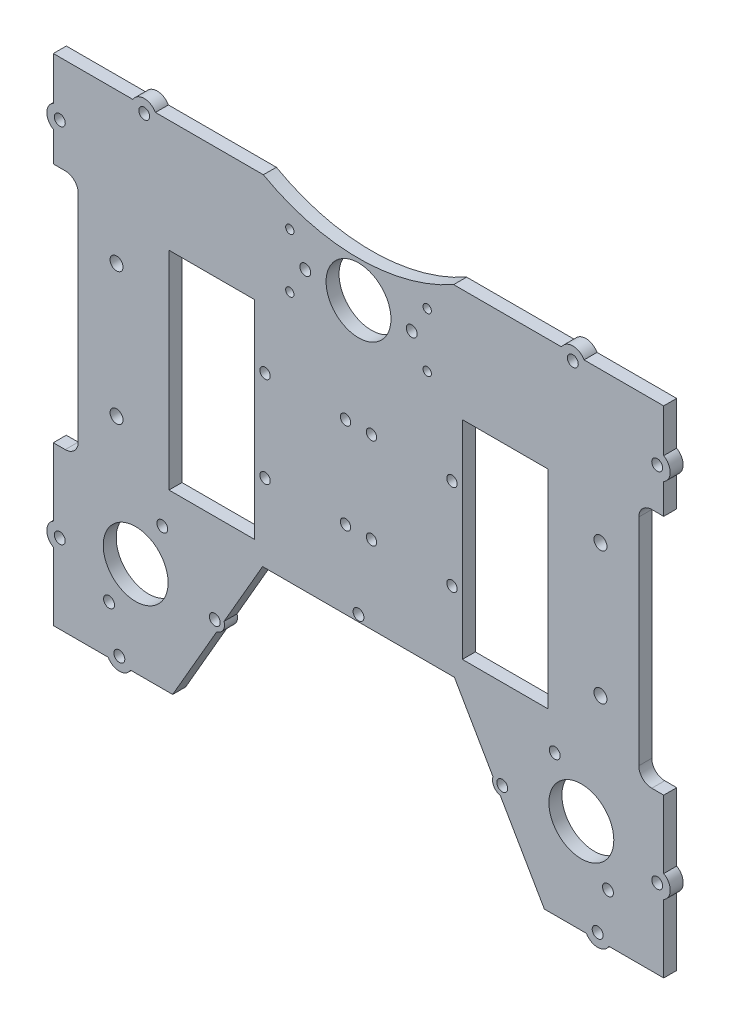
SolidWorks part; units mm, degrees
ref_plane "Front Plane" through (0, 0, 0) normal (0, 0, 1) x (1, 0, 0)
ref_plane "Top Plane" through (0, 0, 0) normal (0, 1, 0) x (1, 0, 0)
ref_plane "Right Plane" through (0, 0, 0) normal (1, 0, 0) x (0, 0, -1)
sketch "Sketch2" plane through (0, 0, 0) normal (0, 0, 1) x (1, 0, 0)
  line L0 (118.8549, -90.2648) -> (131.3549, -68.6142)
  line L1 (131.3549, -68.6142) -> (131.3549, -34.0686)
  line L2 (131.3549, -23.1598) -> (131.3549, 57.175)
  line L3 (131.3549, 68.0837) -> (131.3549, 77.6294)
  line L4 (118.8549, 99.28) -> (102.5756, 108.6789)
  line L5 (93.1284, 114.1332) -> (71.1618, 126.8156)
  line L6 (-68.452, 126.8156) -> (-90.4186, 114.1332)
  line L7 (-99.8658, 108.6789) -> (-116.1451, 99.28)
  line L8 (-128.6451, 77.6294) -> (-128.6451, 68.0837)
  line L9 (-128.6451, 57.175) -> (-128.6451, -23.1598)
  line L10 (-128.6451, -34.0686) -> (-128.6451, -68.6142)
  line L11 (-128.6451, -68.6142) -> (-116.1451, -90.2648)
  line L12 (-116.1451, -90.2648) -> (-48.6451, -129.236)
  line L13 (-48.6451, -129.236) -> (51.3549, -129.236)
  line L14 (51.3549, -129.236) -> (118.8549, -90.2648)
  line L15 (-90.4186, 114.1332) -> (-99.8658, 108.6789)
  line L16 (-128.6451, 68.0837) -> (-128.6451, 57.175)
  line L17 (-128.6451, -23.1598) -> (-128.6451, -34.0686)
  line L18 (131.3549, 68.0837) -> (131.3549, 57.175)
  line L19 (93.1284, 114.1332) -> (102.5756, 108.6789)
  line L20 (131.3549, -23.1598) -> (131.3549, -34.0686)
  arc A2 (131.3549, 77.6294) -> (118.8549, 99.28) centre (106.3549, 77.6294) ccw
  arc A4 (71.1618, 126.8156) -> (69.8628, 127.3391) centre (68.6618, 122.4855) ccw
  arc A5 (-67.153, 127.3391) -> (69.8628, 127.3391) centre (1.3549, 141.7152) ccw
  arc A6 (-67.153, 127.3391) -> (-68.452, 126.8156) centre (-65.952, 122.4855) ccw
  arc A8 (-116.1451, 99.28) -> (-128.6451, 77.6294) centre (-103.6451, 77.6294) ccw
extrude "Boss-Extrude1" add sketch "Sketch2" along normal blind 5
sketch "Sketch4" plane through (0, 0, 5) normal (0, 0, 1) x (1, 0, 0)
  line L0 (1.3549, 141.7152) -> (1.3549, 46.7152) construction
  line L11 (51.3549, -129.236) -> (118.8549, -90.2648)
  line L12 (118.8549, -90.2648) -> (131.3549, -68.6142)
  line L13 (131.3549, -68.6142) -> (131.3549, 77.6294)
  line L14 (118.8549, 99.28) -> (71.1618, 126.8156)
  line L15 (-68.452, 126.8156) -> (-116.1451, 99.28)
  line L16 (-128.6451, 77.6294) -> (-128.6451, -68.6142)
  line L17 (-128.6451, -68.6142) -> (-116.1451, -90.2648)
  line L18 (-116.1451, -90.2648) -> (-48.6451, -129.236)
  line L19 (-48.6451, -129.236) -> (51.3549, -129.236)
  line L23 (76.3249, 123.8347) -> (71.1618, 126.8156)
  line L24 (-68.452, 126.8156) -> (-73.6152, 123.8347)
  arc A1 (-73.6152, 123.8347) -> (76.3249, 123.8347) centre (1.3549, 121.7152) ccw
  arc A7 (131.3549, 77.6294) -> (118.8549, 99.28) centre (106.3549, 77.6294) ccw
  arc A8 (71.1618, 126.8156) -> (69.8628, 127.3391) centre (68.6618, 122.4855) ccw
  arc A9 (-67.153, 127.3391) -> (69.8628, 127.3391) centre (1.3549, 141.7152) ccw
  arc A10 (-67.153, 127.3391) -> (-68.452, 126.8156) centre (-65.952, 122.4855) ccw
  arc A11 (-116.1451, 99.28) -> (-128.6451, 77.6294) centre (-103.6451, 77.6294) ccw
  arc A13 (71.1618, 126.8156) -> (69.8628, 127.3391) centre (68.6618, 122.4855) ccw
  arc A15 (-67.153, 127.3391) -> (-68.452, 126.8156) centre (-65.952, 122.4855) ccw
  arc A17 (-67.153, 127.3391) -> (69.8628, 127.3391) centre (1.3549, 141.7152) ccw
  dimension "D1" = 150
  dimension "D2" = 20
  dimension "D3" = 0
extrude "Cut-Extrude1" cut sketch "Sketch4" against normal blind 5
fillet "Fillet1" radius 10 2 edges at (76.3249, 123.8347, 2.5) (-73.6152, 123.8347, 2.5)
sketch "Sketch6" plane through (0, 0, 5) normal (0, 0, 1) x (1, 0, 0)
  line L0 (-128.6451, -68.6142) -> (-128.6451, -169.9521)
  line L1 (-128.6451, -169.9521) -> (131.3549, -169.9521)
  line L2 (131.3549, -68.6142) -> (131.3549, -169.9521)
  line L12 (118.8549, 99.28) -> (90.1091, 115.8764)
  line L13 (-87.3994, 115.8764) -> (-116.1451, 99.28)
  line L14 (-128.6451, 77.6294) -> (-128.6451, -68.6142)
  line L15 (-128.6451, -68.6142) -> (-116.1451, -90.2648)
  line L16 (-116.1451, -90.2648) -> (-48.6451, -129.236)
  line L17 (-48.6451, -129.236) -> (51.3549, -129.236)
  line L18 (51.3549, -129.236) -> (118.8549, -90.2648)
  line L19 (118.8549, -90.2648) -> (131.3549, -68.6142)
  line L20 (131.3549, -68.6142) -> (131.3549, 77.6294)
  line L24 (-128.6451, -68.6142) -> (-116.1451, -90.2648)
  line L25 (-116.1451, -90.2648) -> (-48.6451, -129.236)
  line L26 (-48.6451, -129.236) -> (51.3549, -129.236)
  line L27 (51.3549, -129.236) -> (118.8549, -90.2648)
  line L28 (118.8549, -90.2648) -> (131.3549, -68.6142)
  arc A5 (90.1091, 115.8764) -> (75.2557, 108.9219) centre (85.1091, 107.2161) ccw
  arc A6 (-72.5459, 108.9219) -> (75.2557, 108.9219) centre (1.3549, 121.7152) ccw
  arc A7 (-72.5459, 108.9219) -> (-87.3994, 115.8764) centre (-82.3994, 107.2161) ccw
  arc A8 (-116.1451, 99.28) -> (-128.6451, 77.6294) centre (-103.6451, 77.6294) ccw
  arc A9 (131.3549, 77.6294) -> (118.8549, 99.28) centre (106.3549, 77.6294) ccw
  dimension "D1" = 0
extrude "Boss-Extrude2" add sketch "Sketch6" against normal blind 5
sketch "Sketch7" plane through (0, 0, 5) normal (0, 0, 1) x (1, 0, 0)
  line L0 (-116.2134, 18.7152) -> (-116.2151, -61.2848)
  line L3 (118.9232, 18.7152) -> (118.9249, -61.2848)
  line L18 (-71.6451, -21.2848) -> (-128.6451, -21.2848) construction
  line L20 (-128.6451, 77.6294) -> (-128.6451, -169.9521) construction
  line L21 (-116.2134, 18.7152) -> (-116.1451, 99.28)
  line L22 (-116.2151, -61.2848) -> (-116.2151, -169.9521)
  line L23 (-128.6451, -169.9521) -> (131.3549, -169.9521) construction
  line L27 (1.3549, -169.9521) -> (1.3549, -118.8458) construction
  line L28 (74.3549, -21.2848) -> (131.3549, -21.2848) construction
  line L32 (118.9249, -61.2848) -> (118.9249, -169.9521)
  line L33 (118.9232, 18.7152) -> (118.8549, 99.28)
  line L52 (118.9249, -169.9521) -> (131.3549, -169.9521)
  line L57 (118.8549, 99.28) -> (90.1091, 115.8764)
  line L58 (-87.3994, 115.8764) -> (-116.1451, 99.28)
  line L59 (-128.6451, 77.6294) -> (-128.6451, -169.9521)
  line L60 (-128.6451, -169.9521) -> (131.3549, -169.9521)
  line L61 (131.3549, -169.9521) -> (131.3549, 77.6294)
  line L64 (-128.6451, 77.6294) -> (-128.6451, -169.9521)
  line L66 (131.3549, -169.9521) -> (131.3549, 77.6294)
  line L68 (-128.6451, -169.9521) -> (131.3549, -169.9521)
  arc A69 (90.1091, 115.8764) -> (75.2557, 108.9219) centre (85.1091, 107.2161) ccw
  arc A70 (-72.5459, 108.9219) -> (75.2557, 108.9219) centre (1.3549, 121.7152) ccw
  arc A71 (-72.5459, 108.9219) -> (-87.3994, 115.8764) centre (-82.3994, 107.2161) ccw
  arc A72 (-116.1451, 99.28) -> (-128.6451, 77.6294) centre (-103.6451, 77.6294) ccw
  arc A73 (131.3549, 77.6294) -> (118.8549, 99.28) centre (106.3549, 77.6294) ccw
  arc A77 (-116.1451, 99.28) -> (-128.6451, 77.6294) centre (-103.6451, 77.6294) ccw
  arc A78 (131.3549, 77.6294) -> (118.8549, 99.28) centre (106.3549, 77.6294) ccw
  dimension "D11" = 0
extrude "Cut-Extrude3" cut sketch "Sketch7" against normal blind 10
sketch "Sketch8" plane through (0, 0, 5) normal (0, 0, 1) x (1, 0, 0)
  line L0 (1.3549, 46.7152) -> (1.3549, -169.9521) construction
  line L1 (-116.2151, -169.9521) -> (118.9249, -169.9521) construction
  line L3 (-19.1451, -101.2848) -> (21.8549, -101.2848) construction
  arc A0 (-72.5459, 108.9219) -> (75.2557, 108.9219) centre (1.3549, 121.7152) ccw construction
  circle A1 centre (1.3549, -101.2848) radius 12.5
  circle A2 centre (21.8549, -101.2848) radius 2.1
  circle A3 centre (-19.1451, -101.2848) radius 2.1
  dimension "D1" = 25
  dimension "D2" = 4.2
  dimension "D3" = 4.2
  dimension "D4" = 20.5
  dimension "D5" = 20.5
extrude "Cut-Extrude4" cut sketch "Sketch8" against normal blind 10
sketch "Sketch9" plane through (0, 0, 5) normal (0, 0, 1) x (1, 0, 0)
  line L0 (-101.2143, -21.2848) -> (103.924, -21.2848) construction
  line L1 (1.3549, -122.073) -> (1.3549, -169.9521) construction
  line L2 (-116.2151, -169.9521) -> (118.9249, -169.9521) construction
  line L6 (94.0402, -122.073) -> (118.9249, -109.2181)
  line L11 (-116.2151, -102.073) -> (-85.0382, -122.073)
  line L12 (-85.0382, -122.073) -> (94.0402, -122.073)
  line L15 (1.3549, 101.5642) -> (-58.9528, 70.4107) [skipped]
  line L16 (118.9249, 33.6852) -> (61.7912, 70.3364) [skipped]
  line L17 (118.9249, -102.073) -> (122.099, -34.2682) [skipped]
  line L18 (-116.2151, 33.6852) -> (-122.5633, -101.9245) [skipped]
  line L25 (-116.2134, 18.7152) -> (-116.2151, -61.2848)
  line L26 (-116.2134, 18.7152) -> (-116.2151, -61.2848)
  line L27 (118.9249, -61.2848) -> (118.9232, 18.7152)
  line L28 (118.9249, -61.2848) -> (118.9232, 18.7152)
  line L29 (-116.2151, -169.9521) -> (118.9249, -169.9521)
  line L30 (-116.2151, -169.9521) -> (118.9249, -169.9521)
  line L32 (-116.2151, -61.2848) -> (-116.2151, -169.9521)
  line L34 (118.9249, -169.9521) -> (118.9249, -61.2848)
  line L38 (118.9232, 18.7152) -> (118.8549, 99.28)
  line L39 (118.8549, 99.28) -> (90.1091, 115.8764)
  line L40 (-87.3994, 115.8764) -> (-116.1451, 99.28)
  line L41 (-116.1451, 99.28) -> (-116.2134, 18.7152)
  line L45 (-116.2151, -102.073) -> (-116.2151, -169.9521)
  line L47 (118.9249, -169.9521) -> (118.9249, -109.2181)
  arc A0 (1.3549, -154.8094) -> (83.9707, -122.073) centre (1.3549, -34.1939) ccw construction
  arc A4 (90.1091, 115.8764) -> (75.2557, 108.9219) centre (85.1091, 107.2161) ccw
  arc A5 (-72.5459, 108.9219) -> (75.2557, 108.9219) centre (1.3549, 121.7152) ccw
  arc A6 (-72.5459, 108.9219) -> (-87.3994, 115.8764) centre (-82.3994, 107.2161) ccw
  line M59 (-116.2151, -61.2848) -> (-116.2151, -169.9521)
  line M60 (-116.2151, -169.9521) -> (118.9249, -169.9521)
  line M61 (118.9249, -169.9521) -> (118.9249, -61.2848)
  dimension "D1" = 20
  dimension "D2" = 0
extrude "Cut-Extrude5" cut sketch "Sketch9" against normal blind 10 contours L12 L11 L6 M59 M60 M61
fillet "Fillet4" radius 10 2 edges at (118.8549, 99.28, 2.5) (-116.1451, 99.28, 2.5)
sketch "Sketch11" plane through (0, 0, 5) normal (0, 0, 1) x (1, 0, 0)
  line L0 (115.3826, -104.3454) -> (87.748, -122.073)
  line L1 (94.0402, -122.073) -> (-85.0382, -122.073) construction
  line L2 (115.3826, -104.3454) -> (118.9249, -102.073)
  line L3 (118.9249, -61.2848) -> (118.9249, -109.2181) construction
  line L4 (118.9249, -102.073) -> (118.9249, -109.2181)
  line L5 (118.9249, -109.2181) -> (94.0402, -122.073)
  line L6 (94.0402, -122.073) -> (87.748, -122.073)
extrude "Cut-Extrude6" cut sketch "Sketch11" against normal blind 55
sketch "Sketch12" plane through (0, 0, 5) normal (0, 0, 1) x (1, 0, 0)
  line L4 (-87.3994, 115.8764) -> (-87.3994, 35.8764) construction
  line L5 (1.3549, 46.7152) -> (1.3549, 28.9079) construction
  line L6 (90.1091, 115.8764) -> (90.1091, 35.8764) construction
  circle A4 centre (-87.3994, 75.8764) radius 12.5
  circle A5 centre (-87.3994, 96.3764) radius 2.1
  circle A6 centre (-87.3994, 55.3764) radius 2.1
  arc A7 (-72.5459, 108.9219) -> (75.2557, 108.9219) centre (1.3549, 121.7152) ccw construction
  circle A8 centre (90.1091, 55.3764) radius 2.1
  circle A9 centre (90.1091, 75.8764) radius 12.5
  circle A10 centre (90.1091, 96.3764) radius 2.1
  dimension "D2" = 4.2
  dimension "D3" = 4.2
  dimension "D4" = 20.5
  dimension "D5" = 20.5
  dimension "D6" = 40
  dimension "D1" = 25
extrude "Cut-Extrude7" cut sketch "Sketch12" against normal blind 10
sketch "Sketch13" plane through (0, 0, 5) normal (0, 0, 1) x (1, 0, 0)
  line L0 (-116.1817, 56.1137) -> (-113.6817, 56.1137) construction
  line L1 (-116.2134, 18.7152) -> (-116.15, 93.5121) construction
  line L2 (-116.2151, -81.6789) -> (-113.7151, -81.6789) construction
  line L3 (-116.2151, -61.2848) -> (-116.2151, -102.073) construction
  line L4 (-96.1558, -109.0007) -> (-97.5056, -111.1049) construction
  line L6 (-40.4918, -117.073) -> (-40.4918, -119.573) construction
  line L8 (1.3549, -122.073) -> (1.3549, -101.2848) construction
  line L9 (87.748, -122.073) -> (-85.0382, -122.073) construction
  line L11 (43.2016, -117.073) -> (43.2016, -119.573) construction
  line L12 (98.8656, -109.0007) -> (100.2154, -111.1049) construction
  line L13 (118.9249, -81.6789) -> (116.4249, -81.6789) construction
  line L14 (118.8915, 56.1137) -> (116.3915, 56.1137) construction
  circle A1 centre (-97.5056, -111.1049) radius 2.1
  circle A2 centre (-40.4918, -119.573) radius 2.1
  circle A3 centre (-113.7151, -81.6789) radius 2.1
  circle A4 centre (-113.6817, 56.1137) radius 2.0979
  circle A5 centre (116.3915, 56.1137) radius 2.0979
  circle A6 centre (116.4249, -81.6789) radius 2.1
  circle A7 centre (43.2016, -119.573) radius 2.1
  circle A8 centre (100.2154, -111.1049) radius 2.1
  dimension "D1" = 2.5
  dimension "D2" = 2.5
  dimension "D3" = 2.5
  dimension "D4" = 2.5
extrude "Cut-Extrude8" cut sketch "Sketch13" against normal blind 10
sketch "Sketch14" plane through (0, 0, 5) normal (0, 0, 1) x (1, 0, 0)
  line L0 (1.3549, -122.073) -> (1.3549, -77.9491) construction
  line L1 (87.748, -122.073) -> (-85.0382, -122.073) construction
  line L2 (-85.0382, -122.073) -> (-116.2151, -102.073) construction
  line L3 (-116.2151, -61.2848) -> (-116.2151, -102.073) construction
  line L4 (-116.2134, 18.7152) -> (-116.15, 93.5121) construction
  line L6 (-95.2109, -115.5472) -> (-102.5002, -110.8711)
  line L7 (-116.2151, -77.3487) -> (-116.2151, -86.009)
  line L8 (-116.1854, 51.7857) -> (-116.178, 60.4459)
  line L9 (-36.1617, -122.073) -> (-44.8219, -122.073)
  line L10 (38.8714, -122.073) -> (47.5317, -122.073)
  line L11 (118.8952, 51.7857) -> (118.8878, 60.4459)
  line L12 (118.9249, -77.3487) -> (118.9249, -86.009)
  line L13 (97.9206, -115.5472) -> (105.21, -110.8711)
  arc A0 (-116.178, 60.4459) -> (-116.1854, 51.7857) centre (-113.6817, 56.1137) ccw
  arc A1 (-116.2151, -77.3487) -> (-116.2151, -86.009) centre (-113.7151, -81.6789) ccw
  arc A2 (-102.5002, -110.8711) -> (-95.2109, -115.5472) centre (-97.5056, -111.1049) ccw
  arc A3 (-44.8219, -122.073) -> (-36.1617, -122.073) centre (-40.4918, -119.573) ccw
  arc A4 (47.5317, -122.073) -> (38.8714, -122.073) centre (43.2016, -119.573) cw
  arc A5 (105.21, -110.8711) -> (97.9206, -115.5472) centre (100.2154, -111.1049) cw
  arc A6 (118.9249, -77.3487) -> (118.9249, -86.009) centre (116.4249, -81.6789) cw
  arc A7 (118.8878, 60.4459) -> (118.8952, 51.7857) centre (116.3915, 56.1137) cw
  dimension "D1" = 10
  dimension "D2" = 10
  dimension "D3" = 10
  dimension "D4" = 10
extrude "Boss-Extrude3" add sketch "Sketch14" against normal blind 5
sketch "Sketch15" plane through (0, 0, 5) normal (0, 0, 1) x (1, 0, 0)
  circle A0 centre (-25.1096, 25.6797) radius 1.6
  circle A1 centre (-25.1096, 4.7508) radius 1.6
  circle A2 centre (27.8194, 25.6797) radius 1.6
  circle A3 centre (27.8194, 4.7508) radius 1.6
extrude "Cut-Extrude9" cut sketch "Sketch15" against normal blind 10
sketch "Sketch16" plane through (0, 0, 5) normal (0, 0, 1) x (1, 0, 0)
  line L0 (-25.1096, 4.7508) -> (27.8194, 25.6797) construction
  line L1 (1.3549, 121.7152) -> (1.3549, -88.7848) construction
  line L2 (-28.6451, 1.2152) -> (31.3549, 1.2152)
  line L3 (-28.6451, 1.2152) -> (-28.6451, 29.2152)
  line L4 (-28.6451, 29.2152) -> (31.3549, 29.2152)
  line L5 (31.3549, 1.2152) -> (31.3549, 29.2152)
  line L6 (-28.6451, 1.2152) -> (31.3549, 29.2152) construction
  line L7 (-28.6451, 29.2152) -> (31.3549, 1.2152) construction
  arc A0 (-72.5459, 108.9219) -> (75.2557, 108.9219) centre (1.3549, 121.7152) ccw construction
  arc A1 (-72.5459, 108.9219) -> (75.2557, 108.9219) centre (1.3549, 121.7152) ccw
  circle A2 centre (1.3549, -101.2848) radius 12.5 construction
  arc A3 (-73.303, 111.3702) -> (76.0128, 111.3702) centre (1.3549, 104.2152) ccw
  arc A4 (90.1091, 115.8764) -> (75.2557, 108.9219) centre (85.1091, 107.2161) ccw construction
  arc A5 (-72.5459, 108.9219) -> (-87.3994, 115.8764) centre (-82.3994, 107.2161) ccw construction
  arc A6 (76.0128, 111.3702) -> (75.2557, 108.9219) centre (85.1091, 107.2161) ccw
  arc A7 (-72.5459, 108.9219) -> (-73.303, 111.3702) centre (-82.3994, 107.2161) ccw
  point P4 (1.3549, 15.2152)
  dimension "D3" = 150
  dimension "D1" = 60
  dimension "D2" = 28
extrude "Cut-Extrude10" cut sketch "Sketch16" against normal blind 10 contours A1 A7 A3 A6
fillet "Fillet5" radius 15 2 edges at (76.0128, 111.3702, 2.5) (-73.303, 111.3702, 2.5)
sketch "Sketch17" plane through (0, 0, 5) normal (0, 0, 1) x (1, 0, 0)
  circle A0 centre (90.1091, 55.3764) radius 2.1 construction
  circle A1 centre (90.1091, 96.3764) radius 2.1 construction
  circle A2 centre (90.1091, 75.8764) radius 12.5 construction
  circle A3 centre (-87.3994, 55.3764) radius 2.1 construction
  circle A4 centre (-87.3994, 96.3764) radius 2.1 construction
  circle A5 centre (-87.3994, 75.8764) radius 12.5 construction
  circle A6 centre (90.1091, 55.3764) radius 2.1
  circle A7 centre (90.1091, 96.3764) radius 2.1
  circle A8 centre (90.1091, 75.8764) radius 12.5
  circle A9 centre (-87.3994, 55.3764) radius 2.1
  circle A10 centre (-87.3994, 96.3764) radius 2.1
  circle A11 centre (-87.3994, 75.8764) radius 12.5
extrude "Boss-Extrude4" add sketch "Sketch17" against normal blind 5
sketch "Sketch18" plane through (0, 0, 5) normal (0, 0, 1) x (1, 0, 0)
  line L1 (-95.9276, 110.9526) -> (-111.15, 102.1639) construction
  line L2 (-116.1794, 58.8457) -> (-71.1068, 84.8684)
  line L3 (-116.178, 60.4459) -> (-116.15, 93.5121) construction
  line L4 (1.3549, 29.2152) -> (1.3549, 82.3228) construction
  line L5 (-116.178, 60.4459) -> (-116.15, 93.5121)
  line L6 (-95.9276, 110.9526) -> (-111.15, 102.1639)
  line L7 (-116.178, 60.4459) -> (-116.1794, 58.8457)
  line L8 (118.8878, 60.4459) -> (118.8892, 58.8457)
  line L9 (98.6374, 110.9526) -> (113.8598, 102.1639)
  line L10 (118.8878, 60.4459) -> (118.8598, 93.5121)
  line L11 (118.8892, 58.8457) -> (73.8166, 84.8684)
  arc A2 (-111.15, 102.1639) -> (-116.15, 93.5121) centre (-106.15, 93.5037) ccw construction
  arc A3 (-73.4639, 99.0044) -> (-95.9276, 110.9526) centre (-88.4276, 97.9622) ccw construction
  arc A4 (-73.4639, 99.0044) -> (76.1737, 99.0044) centre (1.3549, 104.2152) ccw construction
  arc A5 (-111.15, 102.1639) -> (-116.15, 93.5121) centre (-106.15, 93.5037) ccw
  arc A6 (-73.4639, 99.0044) -> (-71.1068, 84.8684) centre (1.3549, 104.2152) ccw
  arc A7 (-73.4639, 99.0044) -> (-95.9276, 110.9526) centre (-88.4276, 97.9622) ccw
  arc A8 (76.1737, 99.0044) -> (98.6374, 110.9526) centre (91.1374, 97.9622) cw
  arc A9 (76.1737, 99.0044) -> (73.8166, 84.8684) centre (1.3549, 104.2152) cw
  arc A10 (113.8598, 102.1639) -> (118.8598, 93.5121) centre (108.8598, 93.5037) cw
  dimension "D1" = 35
extrude "Cut-Extrude11" cut sketch "Sketch18" against normal blind 5
sketch "Sketch20" plane through (0, 0, 5) normal (0, 0, 1) x (1, 0, 0)
  line L2 (118.8892, 58.8457) -> (118.8878, 60.4459) construction
  line L5 (-116.1854, 51.7857) -> (-116.1794, 58.8457)
  line L6 (-116.178, 60.4459) -> (-116.1794, 58.8457) construction
  line L7 (-116.178, 60.4459) -> (-116.1794, 58.8457)
  line L8 (118.8892, 58.8457) -> (118.8878, 60.4459)
  line L9 (118.8892, 58.8457) -> (118.8952, 51.7857)
  arc A4 (-116.178, 60.4459) -> (-116.1854, 51.7857) centre (-113.6817, 56.1137) ccw construction
  arc A5 (-116.178, 60.4459) -> (-116.1854, 51.7857) centre (-113.6817, 56.1137) ccw
  arc A6 (118.8952, 51.7857) -> (118.8878, 60.4459) centre (116.3915, 56.1137) ccw construction
  arc A7 (118.8952, 51.7857) -> (118.8878, 60.4459) centre (116.3915, 56.1137) ccw
extrude "Cut-Extrude13" cut sketch "Sketch20" against normal blind 5
sketch "Sketch24" plane through (0, 0, 5) normal (0, 0, 1) x (1, 0, 0)
  line L0 (118.9062, 38.7805) -> (116.4062, 38.7805) construction
  line L1 (118.9232, 18.7152) -> (118.8892, 58.8457) construction
  line L2 (118.9099, 34.4525) -> (118.9025, 43.1127)
  line L3 (1.3549, 29.2152) -> (1.3549, 59.457) construction
  line L4 (-116.1964, 38.7805) -> (-113.6964, 38.7805) construction
  line L5 (-116.2001, 34.4525) -> (-116.1927, 43.1127)
  arc A0 (118.9099, 34.4525) -> (118.9025, 43.1127) centre (116.4062, 38.7805) ccw
  arc A1 (-71.1068, 84.8684) -> (73.8166, 84.8684) centre (1.3549, 104.2152) ccw construction
  arc A2 (-116.2001, 34.4525) -> (-116.1927, 43.1127) centre (-113.6964, 38.7805) cw
  dimension "D2" = 10
  dimension "D1" = 2.5
extrude "Boss-Extrude7" add sketch "Sketch24" against normal blind 5
sketch "Sketch25" plane through (0, 0, 5) normal (0, 0, 1) x (1, 0, 0)
  circle A0 centre (-113.6964, 38.7805) radius 2.1
  circle A1 centre (116.4062, 38.7805) radius 2.1
  dimension "D1" = 4.2
  dimension "D2" = 4.2
extrude "Cut-Extrude15" cut sketch "Sketch25" against normal blind 5
sketch "Sketch26" plane through (0, 0, 5) normal (0, 0, 1) x (1, 0, 0)
  line L0 (28.8549, -122.073) -> (38.8714, -122.073)
  line L1 (1.3549, -122.073) -> (1.3549, -182.073) construction
  line L3 (-116.2151, -102.073) -> (-116.2151, -152.073)
  line L4 (-151.1719, -152.073) -> (156.005, -152.073) construction
  line L5 (-56.1451, -152.073) -> (-26.1451, -122.073)
  line L7 (-56.1451, -152.073) -> (-105.2952, -152.073)
  line L10 (58.8549, -152.073) -> (28.8549, -122.073)
  line L11 (58.8549, -152.073) -> (108.005, -152.073)
  line L21 (-116.2151, -152.073) -> (-105.2952, -152.073)
  line L22 (118.9249, -102.073) -> (118.9249, -152.073)
  line L23 (118.9249, -152.073) -> (108.005, -152.073)
  line L31 (-71.1068, 84.8684) -> (-116.1794, 58.8457)
  line L32 (-116.2134, 18.7152) -> (-116.2151, -61.2848)
  line L33 (-116.2134, 18.7152) -> (-116.2151, -61.2848)
  line L34 (-116.2151, -102.073) -> (-102.5002, -110.8711)
  line L35 (-116.2151, -102.073) -> (-102.5002, -110.8711)
  line L36 (-95.2109, -115.5472) -> (-85.0382, -122.073)
  line L37 (-95.2109, -115.5472) -> (-85.0382, -122.073)
  line L38 (-85.0382, -122.073) -> (-44.8219, -122.073)
  line L39 (-85.0382, -122.073) -> (-44.8219, -122.073)
  line L40 (-36.1617, -122.073) -> (38.8714, -122.073)
  line L41 (-36.1617, -122.073) -> (38.8714, -122.073)
  line L42 (118.9249, -61.2848) -> (118.9232, 18.7152)
  line L43 (118.9249, -61.2848) -> (118.9232, 18.7152)
  line L45 (-116.1794, 58.8457) -> (-116.1927, 43.1127)
  line L46 (-116.2001, 34.4525) -> (-116.2134, 18.7152)
  line L48 (47.5317, -122.073) -> (87.748, -122.073)
  line L49 (47.5317, -122.073) -> (87.748, -122.073)
  line L50 (-116.2151, -61.2848) -> (-116.2151, -77.3487)
  line L51 (-116.2151, -86.009) -> (-116.2151, -102.073)
  line L57 (87.748, -122.073) -> (97.9206, -115.5472)
  line L58 (105.21, -110.8711) -> (118.9249, -102.073)
  line L59 (118.9249, -102.073) -> (118.9249, -86.009)
  line L60 (118.9249, -77.3487) -> (118.9249, -61.2848)
  line L62 (-71.1068, 84.8684) -> (-116.1794, 58.8457)
  line L63 (118.8892, 58.8457) -> (73.8166, 84.8684)
  line L64 (118.9232, 18.7152) -> (118.9099, 34.4525)
  line L65 (118.9025, 43.1127) -> (118.8892, 58.8457)
  line L66 (118.8892, 58.8457) -> (73.8166, 84.8684)
  line L80 (87.748, -122.073) -> (97.9206, -115.5472)
  line L81 (105.21, -110.8711) -> (118.9249, -102.073)
  arc A10 (-102.5002, -110.8711) -> (-95.2109, -115.5472) centre (-97.5056, -111.1049) ccw
  arc A11 (-102.5002, -110.8711) -> (-95.2109, -115.5472) centre (-97.5056, -111.1049) ccw
  arc A12 (-44.8219, -122.073) -> (-36.1617, -122.073) centre (-40.4918, -119.573) ccw
  arc A13 (-44.8219, -122.073) -> (-36.1617, -122.073) centre (-40.4918, -119.573) ccw
  arc A14 (38.8714, -122.073) -> (47.5317, -122.073) centre (43.2016, -119.573) ccw
  arc A15 (38.8714, -122.073) -> (47.5317, -122.073) centre (43.2016, -119.573) ccw
  arc A33 (-116.1927, 43.1127) -> (-116.2001, 34.4525) centre (-113.6964, 38.7805) ccw
  arc A38 (-116.2151, -77.3487) -> (-116.2151, -86.009) centre (-113.7151, -81.6789) ccw
  arc A42 (97.9206, -115.5472) -> (105.21, -110.8711) centre (100.2154, -111.1049) ccw
  arc A43 (118.9249, -86.009) -> (118.9249, -77.3487) centre (116.4249, -81.6789) ccw
  arc A48 (118.9099, 34.4525) -> (118.9025, 43.1127) centre (116.4062, 38.7805) ccw
  arc A51 (-71.1068, 84.8684) -> (73.8166, 84.8684) centre (1.3549, 104.2152) ccw
  arc A63 (97.9206, -115.5472) -> (105.21, -110.8711) centre (100.2154, -111.1049) ccw
  dimension "D1" = 0
  dimension "D4" = 57.5
extrude "Boss-Extrude8" add sketch "Sketch26" against normal blind 5 contours A13 L39 L37 A11 L35 L3 L21 L7 L5 L41 | A63 L80 L49 A15 L0 L10 L11 L23 L22 L81
sketch "Sketch29" plane through (0, 0, 5) normal (0, 0, 1) x (1, 0, 0)
  line L0 (1.3549, 1.2152) -> (1.3549, 29.2152) construction
  line L1 (28.0313, 15.2152) -> (-26.1436, 15.2152) construction
  line L2 (2.3549, 1.2152) -> (0.3549, 1.2152) construction
  circle A1 centre (1.3549, 15.2152) radius 12.5
  circle A2 centre (21.8549, 15.2152) radius 2.1
  circle A3 centre (-19.1451, 15.2152) radius 2.1
  arc A4 (-71.1068, 84.8684) -> (73.8166, 84.8684) centre (1.3549, 104.2152) ccw construction
  dimension "D1" = 25
  dimension "D2" = 4.2
  dimension "D3" = 4.2
  dimension "D4" = 20.5
  dimension "D5" = 20.5
extrude "Cut-Extrude17" cut sketch "Sketch29" against normal blind 5
sketch "Sketch31" plane through (0, 0, 5) normal (0, 0, 1) x (1, 0, 0)
  circle A1 centre (-19.1451, -101.2848) radius 2.1
  circle A2 centre (-19.1451, -101.2848) radius 2.1
  circle A3 centre (21.8549, -101.2848) radius 2.1
  circle A4 centre (21.8549, -101.2848) radius 2.1
  circle A5 centre (1.3549, -101.2848) radius 12.5
  circle A6 centre (1.3549, -101.2848) radius 12.5
  dimension "D1" = 0
  dimension "D2" = 0
  dimension "D3" = 0
extrude "Boss-Extrude10" add sketch "Sketch31" against normal blind 5
sketch "Sketch32" plane through (0, 0, 5) normal (0, 0, 1) x (1, 0, 0)
  circle A1 centre (100.2154, -111.1049) radius 2.1
  circle A2 centre (100.2154, -111.1049) radius 2.1
  circle A3 centre (43.2016, -119.573) radius 2.1
  circle A4 centre (43.2016, -119.573) radius 2.1
  circle A5 centre (-97.5056, -111.1049) radius 2.1
  circle A6 centre (-97.5056, -111.1049) radius 2.1
  circle A7 centre (-40.4918, -119.573) radius 2.1
  circle A8 centre (-40.4918, -119.573) radius 2.1
  dimension "D1" = 0
  dimension "D2" = 0
  dimension "D3" = 0
  dimension "D4" = 0
extrude "Boss-Extrude11" add sketch "Sketch32" against normal blind 5
sketch "Sketch33" plane through (0, 0, 5) normal (0, 0, 1) x (1, 0, 0)
  circle A1 centre (116.4062, 38.7805) radius 2.1
  circle A2 centre (116.4062, 38.7805) radius 2.1
  circle A3 centre (116.4249, -81.6789) radius 2.1
  circle A4 centre (116.4249, -81.6789) radius 2.1
  circle A5 centre (-113.7151, -81.6789) radius 2.1
  circle A6 centre (-113.7151, -81.6789) radius 2.1
  circle A7 centre (-113.6964, 38.7805) radius 2.1
  circle A8 centre (-113.6964, 38.7805) radius 2.1
  dimension "D1" = 0
  dimension "D2" = 0
  dimension "D3" = 0
  dimension "D4" = 0
extrude "Boss-Extrude12" add sketch "Sketch33" against normal blind 5
sketch "Sketch34" plane through (0, 0, 5) normal (0, 0, 1) x (1, 0, 0)
  line L0 (-116.1927, 43.1127) -> (-116.2001, 34.4525)
  line L1 (-116.2151, -86.009) -> (-116.2151, -77.3487)
  line L2 (118.9025, 43.1127) -> (118.9099, 34.4525)
  line L3 (118.9249, -77.3487) -> (118.9249, -86.009)
  arc A0 (118.9099, 34.4525) -> (118.9025, 43.1127) centre (116.4062, 38.7805) ccw construction
  arc A1 (-116.1927, 43.1127) -> (-116.2001, 34.4525) centre (-113.6964, 38.7805) ccw construction
  arc A2 (-116.2151, -77.3487) -> (-116.2151, -86.009) centre (-113.7151, -81.6789) ccw construction
  arc A3 (118.9249, -86.009) -> (118.9249, -77.3487) centre (116.4249, -81.6789) ccw construction
  arc A4 (118.9099, 34.4525) -> (118.9025, 43.1127) centre (116.4062, 38.7805) ccw
  arc A5 (-116.1927, 43.1127) -> (-116.2001, 34.4525) centre (-113.6964, 38.7805) ccw
  arc A6 (-116.2151, -77.3487) -> (-116.2151, -86.009) centre (-113.7151, -81.6789) ccw
  arc A7 (118.9249, -86.009) -> (118.9249, -77.3487) centre (116.4249, -81.6789) ccw
extrude "Cut-Extrude19" cut sketch "Sketch34" against normal blind 5
sketch "Sketch37" plane through (0, 0, 5) normal (0, 0, 1) x (1, 0, 0)
  line L0 (-116.2134, 18.7152) -> (-116.1794, 58.8457) construction
  line L1 (-116.1964, 38.7805) -> (119.9913, 38.7805)
  line L2 (-116.1964, 38.7805) -> (-116.1964, 86.4137)
  line L3 (-116.1964, 86.4137) -> (119.9913, 86.4137)
  line L4 (119.9913, 38.7805) -> (119.9913, 86.4137)
extrude "Cut-Extrude21" cut sketch "Sketch37" against normal blind 10
sketch "Sketch38" plane through (0, 0, 5) normal (0, 0, 1) x (1, 0, 0)
  line L0 (1.3549, -122.073) -> (1.3549, -152.073) construction
  line L1 (-26.1451, -122.073) -> (28.8549, -122.073) construction
  line L2 (-35.5955, -92.073) -> (33.754, -92.073)
  line L3 (-70.2365, -152.073) -> (-35.5955, -92.073)
  line L4 (-116.2151, -152.073) -> (-56.1451, -152.073) construction
  line L5 (-56.1451, -152.073) -> (58.8549, -152.073) construction
  line L6 (-0.9207, -92.073) -> (-0.9175, -92.116) construction
  line L7 (72.9463, -152.073) -> (38.3053, -92.073)
  line L8 (58.8549, -152.073) -> (28.8549, -122.073) construction
  line L9 (-56.1451, -152.073) -> (-26.1451, -122.073) construction
  line L10 (58.8549, -152.073) -> (28.8549, -122.073)
  line L11 (-26.1451, -122.073) -> (28.8549, -122.073)
  line L12 (-56.1451, -152.073) -> (-26.1451, -122.073)
  line L13 (118.9249, -152.073) -> (58.8549, -152.073) construction
  line L14 (72.9463, -152.073) -> (58.8549, -152.073)
  line L15 (-70.2365, -152.073) -> (-56.1451, -152.073)
  line L16 (33.754, -92.073) -> (38.3053, -92.073)
  arc A2 (1.3549, -92.073) -> (-0.9175, -92.116) centre (1.3549, -152.073) ccw
  point P8 (1.3549, -93.3151)
  dimension "D2" = 120
extrude "Cut-Extrude22" cut sketch "Sketch38" against normal blind 10
sketch "Sketch41" plane through (0, 0, 5) normal (0, 0, 1) x (1, 0, 0)
  line L0 (-35.5955, -92.073) -> (-35.5955, -152.073) construction
  line L1 (-35.5955, -152.073) -> (-116.2151, -152.073) construction
  line L2 (-35.5955, -92.073) -> (-116.2151, -92.073) construction
  line L3 (-116.2151, -61.2848) -> (-116.2151, -152.073) construction
  line L4 (-116.2151, -92.073) -> (-35.5955, -152.073) construction
  line L5 (1.3549, -92.073) -> (1.3549, -119.9712) construction
  line L6 (-35.5955, -92.073) -> (38.3053, -92.073) construction
  circle A1 centre (87.197, -115.686) radius 12.5
  circle A2 centre (97.447, -133.4395) radius 2.1
  circle A3 centre (76.947, -97.9325) radius 2.1
  circle A7 centre (-74.2372, -97.9325) radius 2.1
  circle A8 centre (-94.7372, -133.4395) radius 2.1
  circle A9 centre (-84.4872, -115.686) radius 12.5
extrude "Cut-Extrude23" cut sketch "Sketch41" against normal blind 10
sketch "Sketch43" plane through (0, 0, 5) normal (0, 0, 1) x (1, 0, 0)
  line L0 (-38.6451, -44.573) -> (-71.6451, -44.573) construction
  line L1 (-38.6451, -22.073) -> (-38.6451, -67.073) construction
  line L2 (1.3549, -92.073) -> (1.3549, -77.416) construction
  line L3 (-71.6451, -84.573) -> (-38.6451, -84.573)
  line L4 (-71.6451, -84.573) -> (-71.6451, -4.573)
  line L5 (-71.6451, -4.573) -> (-38.6451, -4.573)
  line L6 (-38.6451, -84.573) -> (-38.6451, -4.573)
  line L7 (-71.6451, -84.573) -> (-38.6451, -4.573) construction
  line L8 (-71.6451, -4.573) -> (-38.6451, -84.573) construction
  line L9 (-35.5955, -92.073) -> (38.3053, -92.073) construction
  line L10 (74.3549, -4.573) -> (41.3549, -84.573) construction
  line L11 (74.3549, -84.573) -> (41.3549, -4.573) construction
  line L12 (41.3549, -44.573) -> (74.3549, -44.573) construction
  line L13 (41.3549, -84.573) -> (41.3549, -4.573)
  line L14 (74.3549, -4.573) -> (41.3549, -4.573)
  line L15 (74.3549, -84.573) -> (74.3549, -4.573)
  line L16 (74.3549, -84.573) -> (41.3549, -84.573)
  circle A0 centre (-34.6451, -27.073) radius 2
  circle A1 centre (-3.6451, -27.073) radius 2
  circle A2 centre (6.3549, -27.073) radius 2
  circle A3 centre (37.3549, -27.073) radius 2
  circle A4 centre (-34.6451, -62.073) radius 2
  circle A5 centre (-3.6451, -62.073) radius 2
  circle A6 centre (6.3549, -62.073) radius 2
  circle A7 centre (37.3549, -62.073) radius 2
  point P4 (-55.1451, -44.573)
  point P19 (57.8549, -44.573)
  dimension "D1" = 33
  dimension "D2" = 80
extrude "Cut-Extrude24" cut sketch "Sketch43" against normal blind 10
sketch "Sketch44" plane through (0, 0, 5) normal (0, 0, 1) x (1, 0, 0)
  circle A0 centre (-91.8451, -19.073) radius 2.5
  circle A1 centre (-91.8451, -70.073) radius 2.5
  circle A2 centre (94.5549, -19.073) radius 2.5
  circle A3 centre (94.5549, -70.073) radius 2.5
extrude "Cut-Extrude25" cut sketch "Sketch44" against normal blind 10
sketch "Sketch45" plane through (0, 0, 5) normal (0, 0, 1) x (1, 0, 0)
  line L0 (-116.2151, -44.573) -> (-110.3151, -44.573) construction
  line L1 (-110.3151, -6.573) -> (-110.3151, -82.573) construction
  line L2 (-109.6151, -82.573) -> (-109.6151, -6.573) construction
  line L3 (-119.9151, -91.0658) -> (-106.6151, -91.0658)
  line L4 (-119.9151, -91.0658) -> (-119.9151, 1.9198)
  line L5 (-119.9151, 1.9198) -> (-106.6151, 1.9198)
  line L6 (-106.6151, -91.0658) -> (-106.6151, 1.9198)
  line L7 (-119.9151, -91.0658) -> (-106.6151, 1.9198) construction
  line L8 (-119.9151, 1.9198) -> (-106.6151, -91.0658) construction
  line L9 (1.3549, -92.073) -> (1.3549, -121.2371) construction
  line L10 (-35.5955, -92.073) -> (38.3053, -92.073) construction
  line L11 (122.6249, 1.9198) -> (109.3249, -91.0658) construction
  line L12 (122.6249, -91.0658) -> (109.3249, 1.9198) construction
  line L13 (118.9249, -44.573) -> (113.0249, -44.573) construction
  line L14 (109.3249, -91.0658) -> (109.3249, 1.9198)
  line L15 (122.6249, 1.9198) -> (109.3249, 1.9198)
  line L16 (122.6249, -91.0658) -> (122.6249, 1.9198)
  line L17 (122.6249, -91.0658) -> (109.3249, -91.0658)
  point P5 (-113.2651, -44.573)
  point P22 (115.9749, -44.573)
  dimension "D1" = 3
extrude "Cut-Extrude26" cut sketch "Sketch45" against normal blind 10
fillet "Fillet6" radius 5 4 edges at (109.3249, 1.9198, 2.5) (109.3249, -91.0658, 2.5) (-106.6151, -91.0658, 2.5) (-106.6151, 1.9198, 2.5)
sketch "Sketch46" plane through (0, 0, 5) normal (0, 0, 1) x (1, 0, 0)
  line L0 (-111.196, 17.8505) -> (-116.2134, 17.8505) construction
  line L1 (-116.2134, 18.7152) -> (-116.2138, 1.9198) construction
  line L2 (-111.2151, -121.568) -> (-116.2151, -121.568) construction
  line L3 (-116.2151, -126.568) -> (-116.2151, -116.568) construction
  line L4 (-90.7701, -147.073) -> (-90.7701, -152.073) construction
  line L5 (-116.2151, -152.073) -> (-70.2365, -152.073) construction
  line L6 (-56.1747, -117.7171) -> (-51.8445, -120.2171) construction
  line L7 (-70.2365, -152.073) -> (-35.5955, -92.073) construction
  line L8 (1.3553, -87.073) -> (1.3549, -92.073) construction
  line L9 (-35.5955, -92.073) -> (38.3053, -92.073) construction
  line L10 (-75.746, 33.7805) -> (-75.7462, 38.7805) construction
  line L11 (-116.1964, 38.7805) -> (-35.296, 38.7805) construction
  line L12 (-70.2365, -152.073) -> (-58.6451, -152.073) construction
  line L13 (-116.2151, -91.0658) -> (-116.2151, -152.073) construction
  line L14 (-116.2134, 18.7152) -> (-116.1964, 38.7805) construction
  line L15 (-53.2421, -122.6377) -> (-50.447, -117.7965)
  line L16 (-95.1002, -152.073) -> (-86.44, -152.073)
  line L17 (-116.2151, -117.2379) -> (-116.2151, -125.8981)
  line L18 (-116.2134, 18.7152) -> (-116.2135, 13.5254)
  line L19 (-116.2134, 18.7152) -> (-116.2105, 22.1773)
  line L20 (-80.0762, 38.7805) -> (-71.416, 38.7805)
  line L23 (93.4799, -147.073) -> (93.4799, -152.073) construction
  line L24 (98.4799, -147.073) -> (88.4799, -147.073) construction
  line L25 (113.9249, -121.568) -> (118.9249, -121.5694) construction
  line L26 (113.9249, -116.568) -> (113.9249, -126.568) construction
  line L33 (118.9249, -91.0658) -> (118.9249, -152.073) construction
  line L34 (-58.6451, -152.063) -> (-70.2466, -152.061) construction
  line L37 (72.9463, -152.073) -> (38.3053, -92.073) construction
  line L38 (113.9058, 17.8505) -> (118.9058, 17.8505) construction
  line L40 (78.4558, 33.7805) -> (78.4558, 38.7805) construction
  line L41 (74.1257, 33.7805) -> (82.7859, 33.7805) construction
  line L42 (118.9249, -152.073) -> (72.9463, -152.073) construction
  line L43 (118.9232, 18.7152) -> (118.9062, 38.7805) construction
  line L44 (118.9232, 18.7152) -> (118.9236, 1.9198) construction
  line L45 (38.0058, 38.7805) -> (118.9062, 38.7805) construction
  line L46 (55.9519, -122.6377) -> (53.1568, -117.7965)
  line L47 (97.81, -152.073) -> (89.1498, -152.073)
  line L48 (118.9249, -117.2386) -> (118.9249, -125.8988)
  line L49 (118.9232, 18.7152) -> (118.9203, 22.1722)
  line L50 (118.9232, 18.7152) -> (118.9233, 13.5305)
  line L51 (74.1257, 38.7805) -> (82.7859, 38.7805)
  arc A0 (-71.416, 38.7805) -> (-80.0762, 38.7805) centre (-75.7461, 36.2805) ccw
  arc A1 (-116.2105, 22.1773) -> (-116.2135, 13.5254) centre (-113.7047, 17.8505) ccw
  arc A2 (-116.2151, -117.2379) -> (-116.2151, -125.8981) centre (-113.7151, -121.568) ccw
  arc A3 (-95.1002, -152.073) -> (-86.44, -152.073) centre (-90.7701, -149.573) ccw
  arc A4 (-53.2421, -122.6377) -> (-50.447, -117.7965) centre (-54.0096, -118.9671) ccw
  arc A7 (-58.6551, -152.073) -> (-58.6551, -152.063) centre (1.3449, -152.073) cw
  arc A13 (-58.6451, -152.063) -> (-58.6451, -152.073) centre (1.3549, -152.073) ccw
  arc A14 (53.1568, -117.7965) -> (55.9519, -122.6377) centre (56.7194, -118.9671) ccw
  arc A15 (89.1498, -152.073) -> (97.81, -152.073) centre (93.4799, -149.573) ccw
  arc A16 (118.9249, -125.8988) -> (118.9249, -117.2386) centre (116.4249, -121.5687) ccw
  arc A17 (118.9233, 13.5305) -> (118.9203, 22.1722) centre (116.4058, 17.8505) ccw
  arc A18 (82.7859, 38.7805) -> (74.1257, 38.7805) centre (78.4558, 36.2805) ccw
  dimension "D1" = 10
  dimension "D2" = 10
  dimension "D3" = 7.5
  dimension "D4" = 10
  dimension "D5" = 10
  dimension "D6" = 7.5
  dimension "D7" = 10
  dimension "D8" = 10
  dimension "D9" = 10
  dimension "D10" = 10
extrude "Boss-Extrude14" add sketch "Sketch46" against normal blind 5 contours L19 A1 L18 | L20 A0 | L17 A2 | L46 A14 | L47 A15 | L48 A16 | L50 A17 L49 | L51 A18 | A3 L16 | A4 L15
sketch "Sketch47" plane through (0, 0, 5) normal (0, 0, 1) x (1, 0, 0)
  circle A1 centre (-75.7461, 36.2805) radius 2.1001
  circle A2 centre (-113.7151, -121.568) radius 2.1
  circle A3 centre (-90.7701, -149.573) radius 2.1
  circle A4 centre (-54.0096, -118.9671) radius 2.1
  circle A5 centre (56.7194, -118.9671) radius 2.1
  circle A6 centre (93.4799, -149.573) radius 2.1
  circle A7 centre (116.4249, -121.5687) radius 2.1007
  circle A8 centre (116.4058, 17.8505) radius 2.1
  circle A9 centre (78.4558, 36.2805) radius 2.1
  circle A10 centre (-113.7047, 17.8505) radius 2.1
extrude "Cut-Extrude27" cut sketch "Sketch47" against normal blind 5
sketch "Sketch48" plane through (0, 0, 5) normal (0, 0, 1) x (1, 0, 0)
  line L0 (1.3553, -87.073) -> (1.3549, -92.073) construction
  line L1 (-35.5955, -92.073) -> (38.3053, -92.073) construction
  circle A0 centre (1.3551, -89.573) radius 2.1002
extrude "Cut-Extrude28" cut sketch "Sketch48" against normal blind 5
sketch "Sketch49" plane through (0, 0, 5) normal (0, 0, 1) x (1, 0, 0)
  line L0 (-80.0762, 38.7805) -> (-71.416, 38.7805)
  line L1 (74.1257, 38.7805) -> (82.7859, 38.7805)
  arc A0 (-71.416, 38.7805) -> (-80.0762, 38.7805) centre (-75.7461, 36.2805) ccw construction
  arc A1 (82.7859, 38.7805) -> (74.1257, 38.7805) centre (78.4558, 36.2805) ccw construction
  arc A2 (-71.416, 38.7805) -> (-80.0762, 38.7805) centre (-75.7461, 36.2805) ccw
  arc A3 (82.7859, 38.7805) -> (74.1257, 38.7805) centre (78.4558, 36.2805) ccw
extrude "Cut-Extrude29" cut sketch "Sketch49" against normal blind 5
sketch "Sketch50" plane through (0, 0, 5) normal (0, 0, 1) x (1, 0, 0)
  circle A0 centre (-75.7461, 36.2805) radius 2.1001 construction
  circle A1 centre (78.4558, 36.2805) radius 2.1 construction
  circle A2 centre (-75.7461, 36.2805) radius 2.1001
  circle A3 centre (78.4558, 36.2805) radius 2.1
extrude "Boss-Extrude15" add sketch "Sketch50" against normal blind 5
sketch "Sketch52" plane through (0, 0, 5) normal (0, 0, 1) x (1, 0, 0)
  line L0 (88.2363, 38.7805) -> (79.5761, 38.7805) construction
  line L1 (38.0058, 38.7805) -> (118.9062, 38.7805) construction
  line L2 (83.9062, 38.7805) -> (83.9062, 33.7805) construction
  line L3 (79.5761, 38.7805) -> (88.2363, 38.7805)
  line L4 (1.3549, 29.2152) -> (1.3549, 71.8467) construction
  line L5 (-81.1964, 38.7805) -> (-81.1964, 33.7805) construction
  line L6 (-85.5265, 38.7805) -> (-76.8663, 38.7805) construction
  line L7 (-76.8663, 38.7805) -> (-85.5265, 38.7805)
  arc A0 (88.2363, 38.7805) -> (79.5761, 38.7805) centre (83.9062, 36.2805) ccw
  arc A1 (-35.296, 38.7805) -> (38.0058, 38.7805) centre (1.3549, 104.2152) ccw construction
  arc A2 (-85.5265, 38.7805) -> (-76.8663, 38.7805) centre (-81.1964, 36.2805) cw
  dimension "D3" = 10
  dimension "D2" = 5
extrude "Boss-Extrude16" add sketch "Sketch52" against normal blind 5
sketch "Sketch53" plane through (0, 0, 5) normal (0, 0, 1) x (1, 0, 0)
  circle A0 centre (83.9062, 36.2805) radius 2.1
  circle A1 centre (-81.1964, 36.2805) radius 2.1
  dimension "D1" = 4.2
  dimension "D2" = 4.2
extrude "Cut-Extrude30" cut sketch "Sketch53" against normal blind 5
